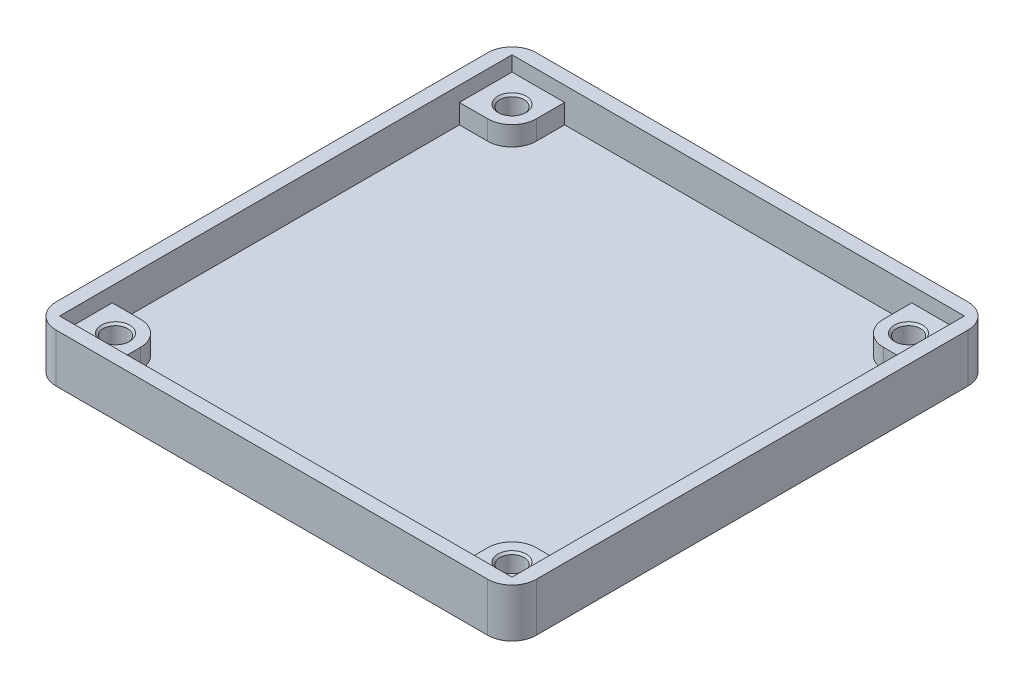
SolidWorks part; units mm, degrees
ref_plane "Front Plane" through (0, 0, 0) normal (0, 0, 1) x (1, 0, 0)
ref_plane "Top Plane" through (0, 0, 0) normal (0, 1, 0) x (1, 0, 0)
ref_plane "Right Plane" through (0, 0, 0) normal (1, 0, 0) x (0, 0, -1)
sketch "Sketch1" plane through (0, 0, 0) normal (0, 1, 0) x (1, 0, 0)
  line L1 (-29.675, -29.675) -> (29.675, -29.675)
  line L2 (-29.675, -29.675) -> (-29.675, 29.675)
  line L3 (-29.675, 29.675) -> (29.675, 29.675)
  line L4 (29.675, -29.675) -> (29.675, 29.675)
  line L5 (-29.675, -29.675) -> (29.675, 29.675) construction
  line L6 (-29.675, 29.675) -> (29.675, -29.675) construction
  point P0 (0, 0)
  dimension "D1" = 59.35
extrude "Boss-Extrude1" add sketch "Sketch1" along normal blind 6 contours L2 L3 L4 L1
sketch "Sketch2" plane through (0, 6, 0) normal (0, 1, 0) x (1, 0, 0)
  line L1 (-24.5, -24.5) -> (24.5, -24.5) construction
  line L2 (-24.5, -24.5) -> (-24.5, 24.5) construction
  line L3 (-24.5, 24.5) -> (24.5, 24.5) construction
  line L4 (24.5, -24.5) -> (24.5, 24.5) construction
  line L5 (-24.5, -24.5) -> (24.5, 24.5) construction
  line L6 (-24.5, 24.5) -> (24.5, -24.5) construction
  circle A4 centre (-24.5, 24.5) radius 1.5
  circle A5 centre (24.5, 24.5) radius 1.5
  circle A6 centre (-24.5, -24.5) radius 1.5
  circle A7 centre (24.5, -24.5) radius 1.5
  point P0 (0, 0)
  dimension "D2" = 3
  dimension "D1" = 49
extrude "Cut-Extrude1" cut sketch "Sketch2" against normal through all
sketch "Sketch3" plane through (0, 6, 0) normal (0, 1, 0) x (1, 0, 0)
  line L0 (-29.675, 29.675) -> (29.675, 29.675) construction
  line L1 (21.425, -27.925) -> (-21.425, -27.925)
  line L2 (27.925, -21.425) -> (27.925, 21.425)
  line L3 (21.425, 27.925) -> (-21.425, 27.925)
  line L4 (-27.925, -21.425) -> (-27.925, 21.425)
  line L5 (-29.675, -29.675) -> (-29.675, 29.675) construction
  line L7 (-27.925, 21.425) -> (-21.425, 21.425)
  line L8 (-21.425, 21.425) -> (-21.425, 27.925)
  line L9 (21.425, 27.925) -> (21.425, 21.425)
  line L10 (21.425, 21.425) -> (27.925, 21.425)
  line L11 (-27.925, -21.425) -> (-21.425, -21.425)
  line L12 (-21.425, -21.425) -> (-21.425, -27.925)
  line L13 (27.925, -21.425) -> (21.425, -21.425)
  line L14 (21.425, -21.425) -> (21.425, -27.925)
  point P0 (0, 0)
  dimension "D1" = 1.75
  dimension "D2" = 6.5
  dimension "D4" = 1.75
  dimension "D5" = 42.85
sketch "Sketch7" plane through (0, 6, 0) normal (0, 1, 0) x (1, 0, 0)
  line L1 (27.95, -27.95) -> (-27.95, -27.95)
  line L2 (27.95, -27.95) -> (27.95, 27.95)
  line L3 (27.95, 27.95) -> (-27.95, 27.95)
  line L4 (-27.95, -27.95) -> (-27.95, 27.95)
  line L5 (27.95, -27.95) -> (-27.95, 27.95) construction
  line L6 (27.95, 27.95) -> (-27.95, -27.95) construction
  point P0 (0, 0)
  dimension "D1" = 55.9
extrude "Cut-Extrude3" cut sketch "Sketch7" against normal blind 1.85
sketch "Sketch8" plane through (0, 4.15, 0) normal (0, 1, 0) x (1, 0, 0)
  line L0 (-27.95, 21.45) -> (-21.45, 21.45)
  line L1 (-27.95, 27.95) -> (-27.95, -27.95) construction
  line L2 (-21.45, 21.45) -> (-21.45, 27.95)
  line L3 (27.95, 27.95) -> (-27.95, 27.95) construction
  line L4 (-21.45, 27.95) -> (21.45, 27.95)
  line L5 (21.45, 27.95) -> (21.45, 21.45)
  line L6 (21.45, 21.45) -> (27.95, 21.45)
  line L7 (27.95, -27.95) -> (27.95, 27.95) construction
  line L8 (27.95, 21.45) -> (27.95, -21.45)
  line L9 (27.95, -27.95) -> (27.95, 27.95) construction
  line L10 (27.95, -21.45) -> (21.45, -21.45)
  line L11 (21.45, -21.45) -> (21.45, -27.95)
  line L12 (-27.95, -27.95) -> (27.95, -27.95) construction
  line L13 (21.45, -27.95) -> (-21.45, -27.95)
  line L14 (-21.45, -27.95) -> (-21.45, -21.45)
  line L15 (-21.45, -21.45) -> (-27.95, -21.45)
  line L16 (-27.95, 27.95) -> (-27.95, -27.95) construction
  line L17 (-27.95, -21.45) -> (-27.95, 21.45)
  dimension "D1" = 6.5
extrude "Cut-Extrude4" cut sketch "Sketch8" against normal blind 2.4
fillet "Fillet1" radius 3 8 edges at (21.45, 2.95, 21.45) (-21.45, 2.95, 21.45) (-21.45, 2.95, -21.45) (21.45, 2.95, -21.45) (-29.675, 3, 29.675) (29.675, 3, 29.675) (29.675, 3, -29.675) (-29.675, 3, -29.675)
chamfer "Chamfer1" distance 0.25 angle 45 4 edges at (24.5, 4.15, 26) (-24.5, 4.15, 26) (24.5, 4.15, -23) (-24.5, 4.15, -23)
